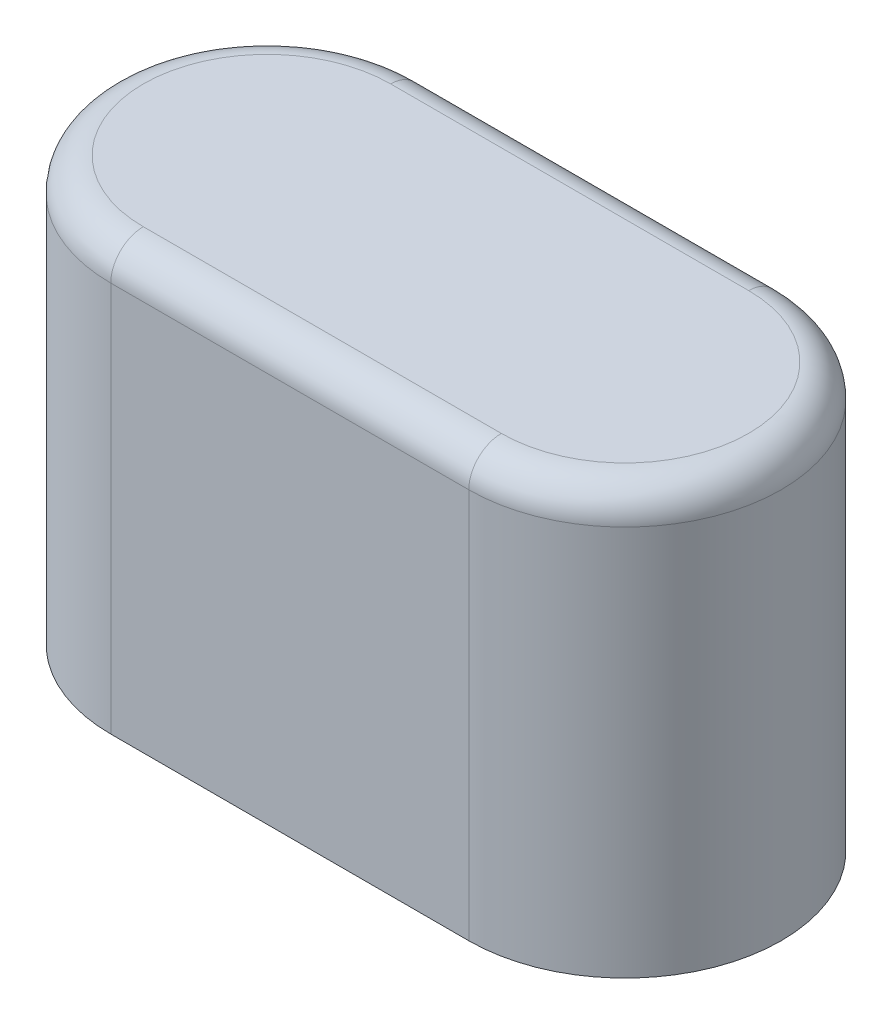
SolidWorks part; units mm, degrees
ref_plane "Front Plane" through (0, 0, 0) normal (0, 0, 1) x (1, 0, 0)
ref_plane "Top Plane" through (0, 0, 0) normal (0, 1, 0) x (1, 0, 0)
ref_plane "Right Plane" through (0, 0, 0) normal (1, 0, 0) x (0, 0, -1)
sketch "Sketch1" plane through (0, 0, 0) normal (0, 1, 0) x (1, 0, 0)
  line L0 (-3.4925, 0) -> (3.4925, 0) construction
  line L1 (-3.4925, 3.048) -> (3.4925, 3.048)
  line L2 (-3.4925, -3.048) -> (3.4925, -3.048)
  arc A0 (-3.4925, 3.048) -> (-3.4925, -3.048) centre (-3.4925, 0) ccw
  arc A1 (3.4925, -3.048) -> (3.4925, 3.048) centre (3.4925, 0) ccw
  point P2 (0, 0)
  dimension "D1" = 3.048
  dimension "D2" = 6.985
extrude "Boss-Extrude1" add sketch "Sketch1" along normal blind 8.255
fillet "Fillet1" radius 0.635 4 edges at (0, 8.255, 3.048) (-6.5405, 8.255, 0) (0, 8.255, -3.048) (6.5405, 8.255, 0)
sketch "Sketch2" plane through (0, 0, 0) normal (0, -1, 0) x (1, 0, 0)
  circle A0 centre (0, 0) radius 1.778
  dimension "D1" = 3.556
extrude "Cut-Extrude3" cut sketch "Sketch2" against normal blind 6.985
